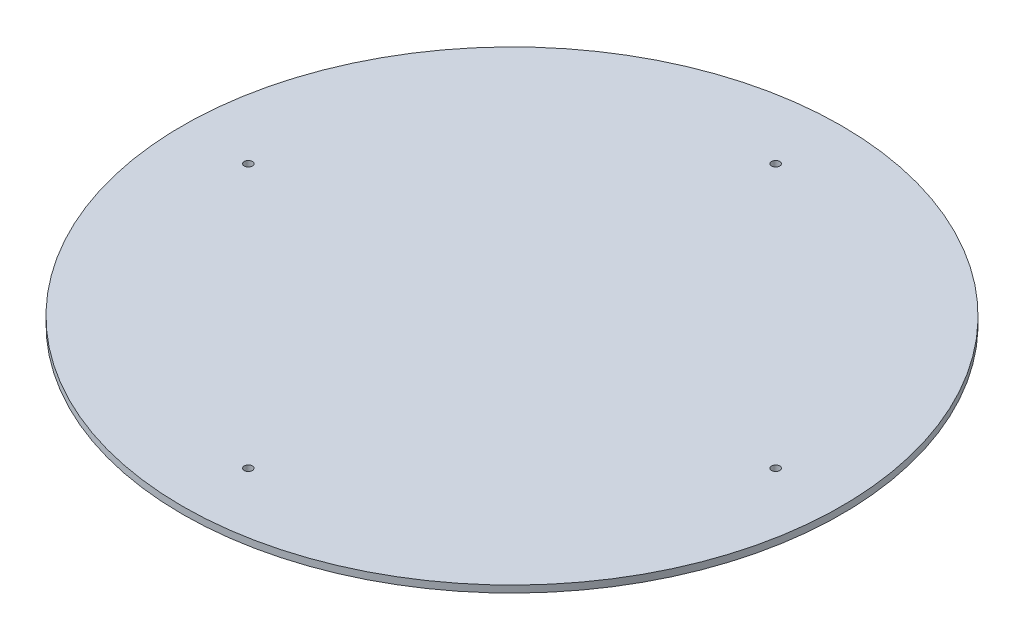
SolidWorks part; units mm, degrees
ref_plane "Front Plane" through (0, 0, 0) normal (0, 0, 1) x (1, 0, 0)
ref_plane "Top Plane" through (0, 0, 0) normal (0, 1, 0) x (1, 0, 0)
ref_plane "Right Plane" through (0, 0, 0) normal (1, 0, 0) x (0, 0, -1)
sketch "Tapa" plane through (0, 0, 0) normal (0, 1, 0) x (1, 0, 0)
  circle A0 centre (0, 0) radius 285
  dimension "D1" = 570
extrude "Saliente-Extruir1" add sketch "Tapa" along normal blind 6
sketch "Croquis2" plane through (0, 0, 0) normal (0, 1, 0) x (1, 0, 0)
  line L0 (0, 0) -> (228.035, 0) construction
  circle A0 centre (228.035, 0) radius 3.5
  circle A1 centre (0, -228.035) radius 3.5
  circle A2 centre (-228.035, 0) radius 3.5
  circle A3 centre (0, 228.035) radius 3.5
  point P13 (0, 0)
  dimension "D2" = 7
  dimension "D1" = 228.035
  dimension "D3" = 4
extrude "Cortar-Extruir4" cut sketch "Croquis2" along normal through all
